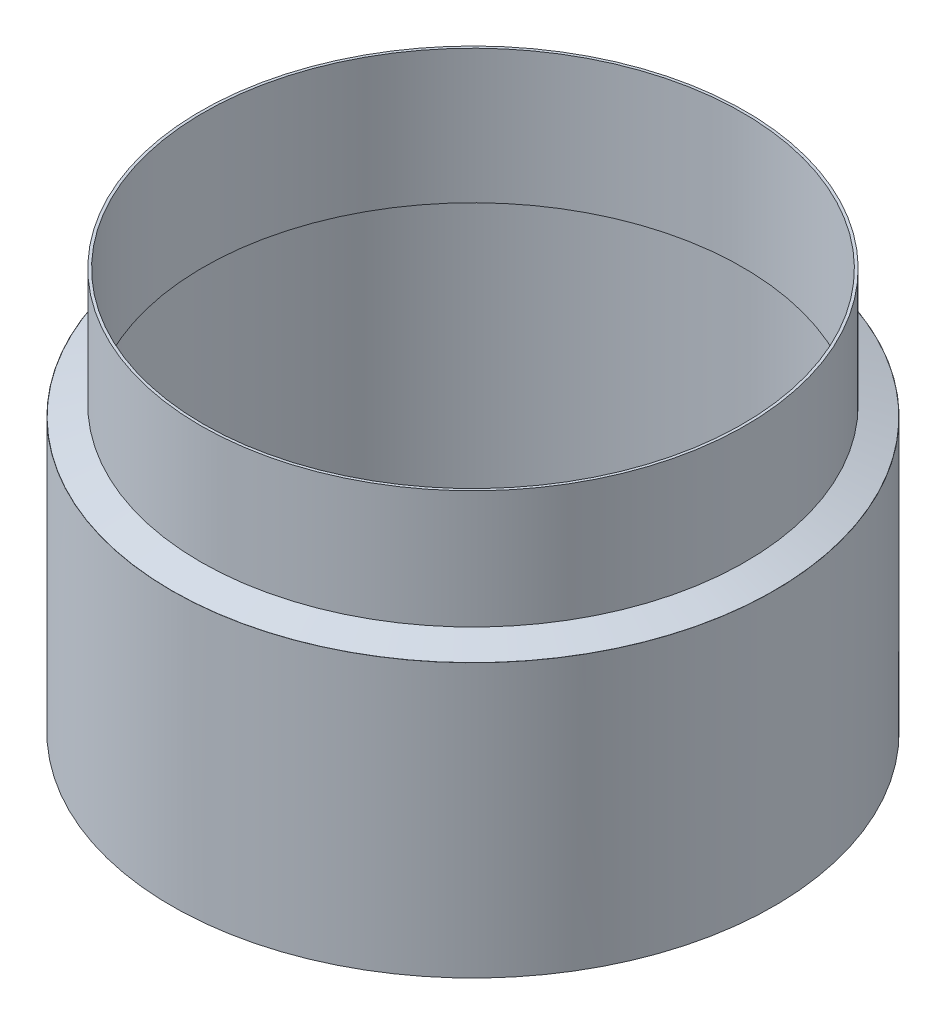
SolidWorks part; units mm, degrees
ref_plane "Front Plane" through (0, 0, 0) normal (0, 0, 1) x (1, 0, 0)
ref_plane "Top Plane" through (0, 0, 0) normal (0, 1, 0) x (1, 0, 0)
ref_plane "Right Plane" through (0, 0, 0) normal (1, 0, 0) x (0, 0, -1)
sketch "Sketch1" plane through (0, 0, 0) normal (0, 1, 0) x (1, 0, 0)
  circle A0 centre (0, 0) radius 40.7
  circle A1 centre (0, 0) radius 40.3
  dimension "D1" = 81.4
  dimension "D2" = 0.4
extrude "Boss-Extrude1" add sketch "Sketch1" along normal blind 20
sketch "Sketch2" plane through (0, 0, 0) normal (0, -1, 0) x (1, 0, 0)
  circle A0 centre (0, 0) radius 44.225
  circle A1 centre (0, 0) radius 45.025
  dimension "D1" = 88.45
  dimension "D2" = 0.8
extrude "Boss-Extrude2" add sketch "Sketch2" along normal blind 40 separate body
sketch "Sketch3" plane through (0, 0, 0) normal (0, 1, 0) x (1, 0, 0)
  circle A0 centre (0, 0) radius 40.7 construction
  circle A1 centre (0, 0) radius 45.025 construction
  circle A2 centre (0, 0) radius 40.7
  circle A3 centre (0, 0) radius 45.025
extrude "Boss-Extrude3" add sketch "Sketch3" along normal blind 0.8
chamfer "Chamfer1" distance 4.3 angle 20 1 edges at (0, 0.8, 40.7)
